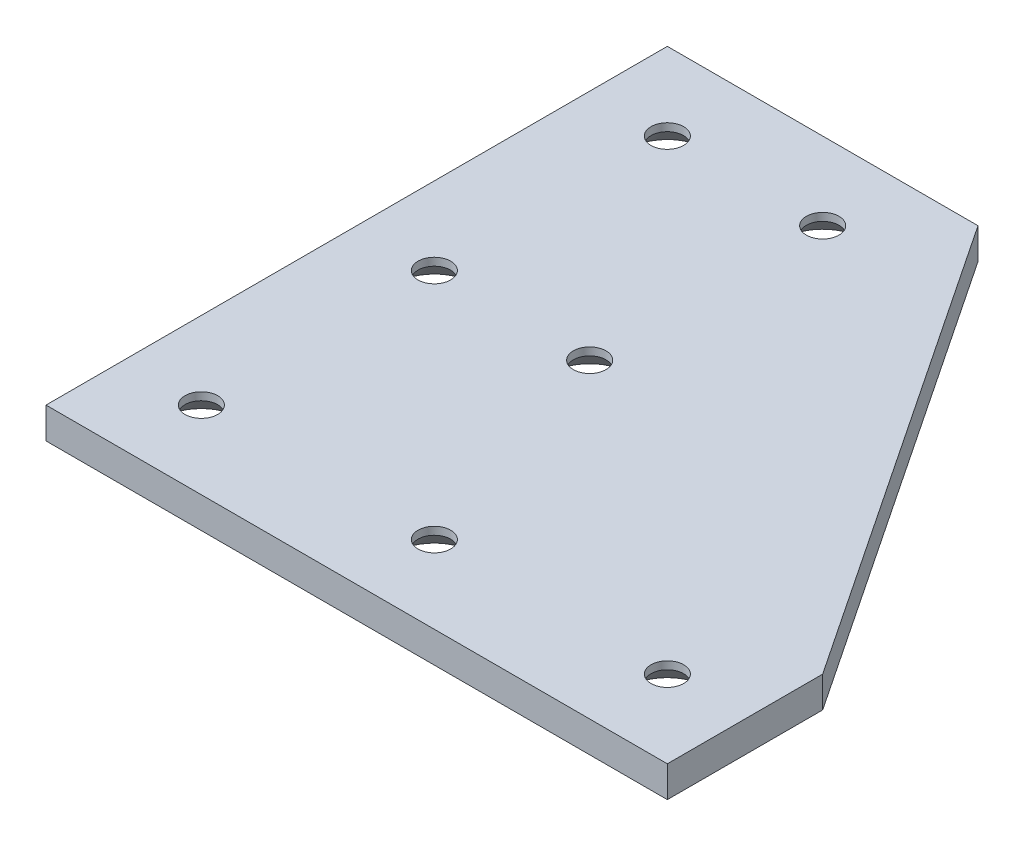
SolidWorks part; units mm, degrees
material "1060 Alloy"
ref_plane "Front Plane" through (0, 0, 0) normal (0, 0, 1) x (1, 0, 0)
ref_plane "Top Plane" through (0, 0, 0) normal (0, 1, 0) x (1, 0, 0)
ref_plane "Right Plane" through (0, 0, 0) normal (1, 0, 0) x (0, 0, -1)
sketch "Sketch1" plane through (0, 0, 0) normal (0, 1, 0) x (1, 0, 0)
  line L0 (0, 0) -> (80, 0)
  line L1 (80, 0) -> (80, 20)
  line L2 (80, 20) -> (40, 80)
  line L3 (40, 80) -> (0, 80)
  line L4 (0, 80) -> (0, 0)
  point P8 (0, 80)
  point P11 (40, 80)
  point P14 (80, 20)
  point P17 (80, 0)
  point P20 (0, 0)
  dimension "D1" = 80
  dimension "D2" = 80
  dimension "D3" = 20
  dimension "D4" = 40
extrude "Boss-Extrude1" add sketch "Sketch1" along normal blind 4
sketch "Sketch2" plane through (0, 4, 0) normal (0, 1, 0) x (1, 0, 0)
  line L0 (0, 0) -> (80, 0) construction
  line L1 (0, 80) -> (0, 0) construction
  line L2 (80, 0) -> (80, 20) construction
  line L3 (40, 80) -> (0, 80) construction
  circle A0 centre (10, 10) radius 2.1
  circle A1 centre (40, 10) radius 2.1
  circle A2 centre (70, 10) radius 2.1
  circle A4 centre (30, 40) radius 2.1
  circle A5 centre (30, 70) radius 2.1
  circle A6 centre (10, 40) radius 2.1
  circle A7 centre (10, 70) radius 2.1
  circle A8 centre (30, 10) radius 2.1 [skipped]
  dimension "D1" = 4.2
  dimension "D3" = 3
  dimension "D2" = 10
  dimension "10" = 10
  dimension "D4" = 10
  dimension "D7" = 10
  dimension "D8" = 10
  dimension "D9" = 20
  dimension "D5" = 2
  dimension "D6" = 3
extrude "Cut-Extrude1" cut sketch "Sketch2" against normal blind 4
chamfer "Chamfer1" distance 3 angle 45 7 edges at (10, 0, -67.9) (30, 0, -67.9) (30, 0, -37.9) (10, 0, -37.9) (10, 0, -7.9) (40, 0, -7.9) (70, 0, -7.9)
fillet "Fillet1" [suppressed] radius 1
